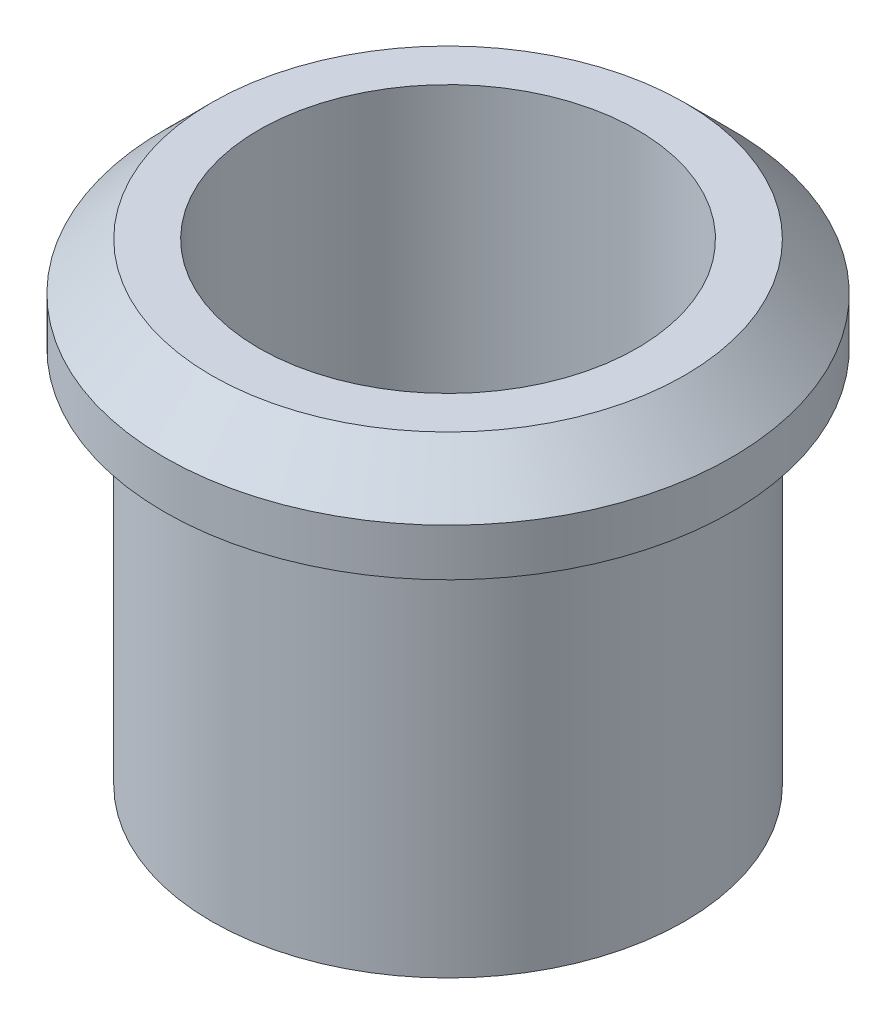
SolidWorks part; units mm, degrees
ref_plane "Front Plane" through (0, 0, 0) normal (0, 0, 1) x (1, 0, 0)
ref_plane "Top Plane" through (0, 0, 0) normal (0, 1, 0) x (1, 0, 0)
ref_plane "Right Plane" through (0, 0, 0) normal (1, 0, 0) x (0, 0, -1)
sketch "Sketch2" plane through (0, 0, 0) normal (0, 1, 0) x (1, 0, 0)
  circle A0 centre (0, 0) radius 2.5
  circle A1 centre (0, 0) radius 2
  dimension "D1" = 5
  dimension "D2" = 4
extrude "Boss-Extrude1" add sketch "Sketch2" along normal blind 4
sketch "Sketch3" plane through (0, 4, 0) normal (0, 1, 0) x (1, 0, 0)
  circle A1 centre (0, 0) radius 2 construction
  circle A3 centre (0, 0) radius 2
  circle A6 centre (0, 0) radius 3
  circle A7 centre (0, 0) radius 3
  dimension "D1" = 1
extrude "Boss-Extrude2" add sketch "Sketch3" along normal blind 1
chamfer "Chamfer1" distance 0.5 angle 45 1 edges at (0, 5, 3)
